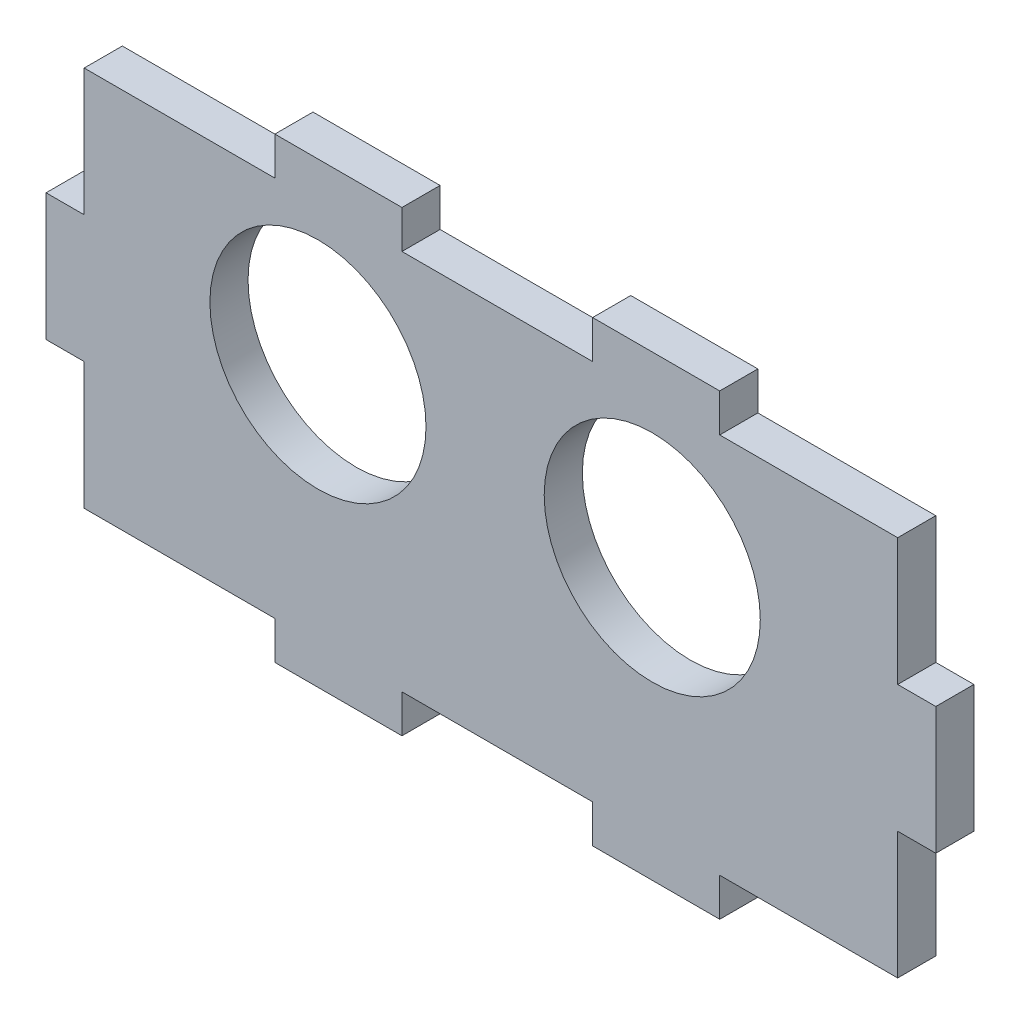
SolidWorks part; units mm, degrees
ref_plane "Plan de face" through (0, 0, 0) normal (0, 0, 1) x (1, 0, 0)
ref_plane "Plan de dessus" through (0, 0, 0) normal (0, 1, 0) x (1, 0, 0)
ref_plane "Plan de droite" through (0, 0, 0) normal (1, 0, 0) x (0, 0, -1)
sketch "Esquisse1" plane through (0, 0, 0) normal (0, 0, 1) x (1, 0, 0)
  line L2 (-38.9012, 0) -> (-23.9012, 0)
  line L3 (-23.9012, 0) -> (-23.9012, 3)
  line L4 (-23.9012, 3) -> (-13.9012, 3)
  line L5 (-13.9012, 3) -> (-13.9012, 0)
  line L6 (-13.9012, 0) -> (1.0988, 0)
  line L7 (1.0988, 0) -> (1.0988, 3)
  line L8 (1.0988, 3) -> (11.0988, 3)
  line L9 (11.0988, 3) -> (11.0988, 0)
  line L10 (11.0988, 0) -> (25.0988, 0)
  line L11 (25.0988, 0) -> (25.0988, -10)
  line L12 (25.0988, -10) -> (28.0988, -10)
  line L13 (28.0988, -10) -> (28.0988, -20)
  line L14 (28.0988, -20) -> (25.0988, -20)
  line L15 (25.0988, -20) -> (25.0988, -30)
  line L16 (25.0988, -30) -> (11.0988, -30)
  line L17 (11.0988, -30) -> (11.0988, -33)
  line L18 (11.0988, -33) -> (1.0988, -33)
  line L19 (1.0988, -33) -> (1.0988, -30)
  line L20 (1.0988, -30) -> (-13.9012, -30)
  line L21 (-13.9012, -30) -> (-13.9012, -33)
  line L22 (-13.9012, -33) -> (-23.9012, -33)
  line L23 (-23.9012, -33) -> (-23.9012, -30)
  line L24 (-23.9012, -30) -> (-38.9012, -30)
  line L26 (-38.9012, 0) -> (-38.9012, -10)
  line L27 (-38.9012, -10) -> (-41.9012, -10)
  line L28 (-41.9012, -10) -> (-41.9012, -20)
  line L29 (-41.9012, -20) -> (-38.9012, -20)
  line L30 (-38.9012, -20) -> (-38.9012, -30)
  circle A0 centre (-20.5105, -11) radius 8.5
  circle A1 centre (5.7895, -11) radius 8.5
  dimension "D24" = 17
  dimension "D25" = 17
  dimension "D1" = 64
  dimension "D2" = 15
  dimension "D3" = 10
  dimension "D4" = 15
  dimension "D5" = 10
  dimension "D6" = 3
  dimension "D7" = 3
  dimension "D8" = 30
  dimension "D9" = 10
  dimension "D10" = 10
  dimension "D11" = 3
  dimension "D12" = 10
  dimension "D13" = 10
  dimension "D14" = 3
  dimension "D15" = 64
  dimension "D16" = 15
  dimension "D17" = 10
  dimension "D18" = 15
  dimension "D19" = 3
  dimension "D20" = 3
  dimension "D21" = 3
  dimension "D22" = 10
  dimension "D23" = 10
  dimension "D26" = 11
  dimension "D27" = 11
  dimension "D28" = 11
  dimension "D29" = 26.3
  dimension "D30" = 3
  dimension "D31" = 3
extrude "Boss.-Extru.1" add sketch "Esquisse1" along normal blind 3
